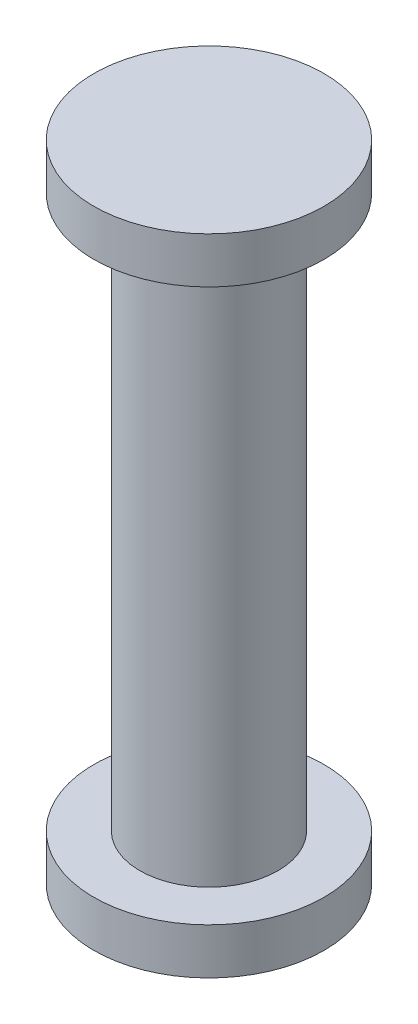
SolidWorks part; units mm, degrees
ref_plane "Front Plane" through (0, 0, 0) normal (0, 0, 1) x (1, 0, 0)
ref_plane "Top Plane" through (0, 0, 0) normal (0, 1, 0) x (1, 0, 0)
ref_plane "Right Plane" through (0, 0, 0) normal (1, 0, 0) x (0, 0, -1)
sketch "Sketch1" plane through (0, 0, 0) normal (0, 0, 1) x (1, 0, 0)
  line L0 (0, 0) -> (0, 14)
  line L1 (0, 14) -> (-2.5, 14)
  line L2 (-2.5, 14) -> (-2.5, 13)
  line L3 (-2.5, 13) -> (-1.5, 13)
  line L4 (-1.5, 13) -> (-1.5, 1)
  line L5 (-1.5, 1) -> (-2.5, 1)
  line L6 (-2.5, 1) -> (-2.5, 0)
  line L7 (-2.5, 0) -> (0, 0)
  point P4 (-1.5, 7)
  dimension "D1" = 14
  dimension "D2" = 1
  dimension "D3" = 2.5
  dimension "D4" = 1.5
revolve "Revolve1" add sketch "Sketch1" angle 360 about L0
